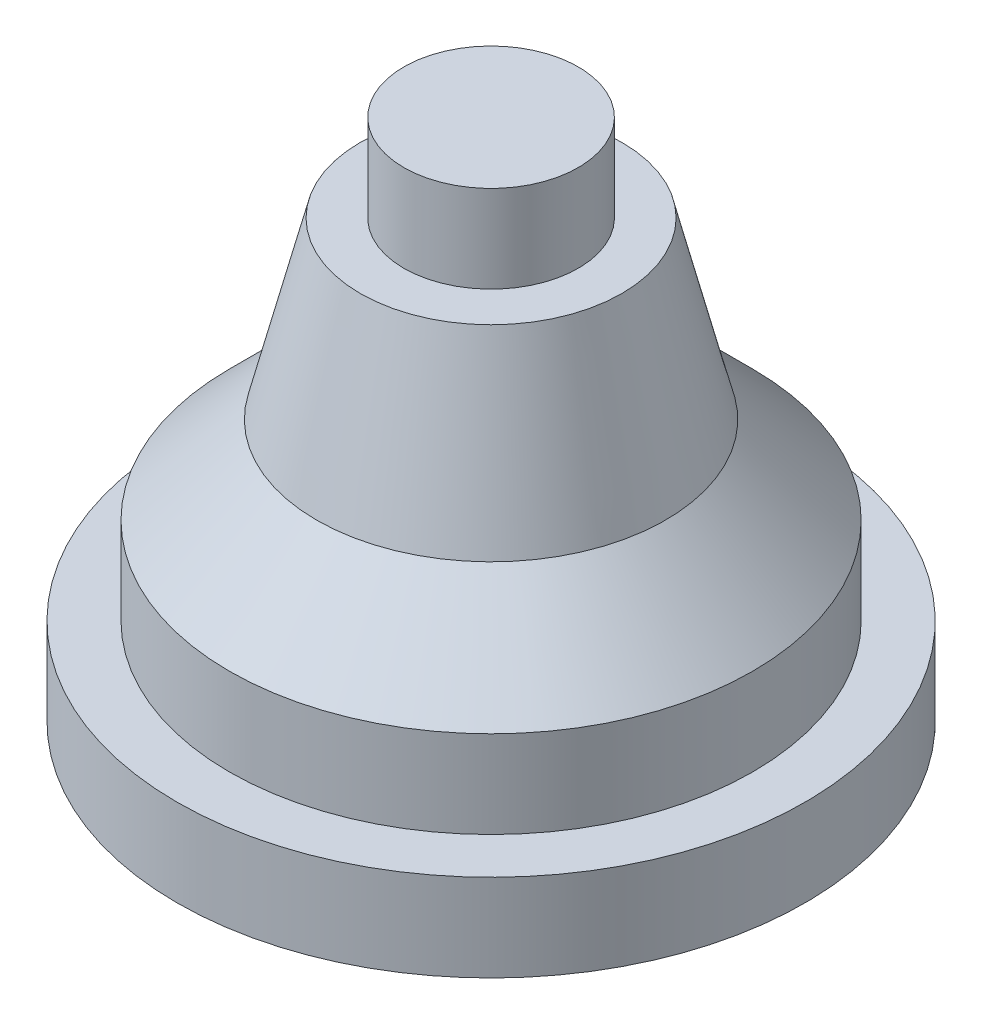
SolidWorks part; units mm, degrees
ref_plane "Plano frontal" through (0, 0, 0) normal (0, 0, 1) x (1, 0, 0)
ref_plane "Plano superior" through (0, 0, 0) normal (0, 1, 0) x (1, 0, 0)
ref_plane "Plano direito" through (0, 0, 0) normal (1, 0, 0) x (0, 0, -1)
sketch "Esboço1" plane through (0, 0, 0) normal (0, 0, 1) x (1, 0, 0)
  line L0 (0, 54.9096) -> (0, -50.9374) construction
  line L1 (0, 75) -> (25, 75)
  line L2 (25, 75) -> (25, 50)
  line L3 (25, 50) -> (37.5, 50)
  line L4 (37.5, 50) -> (50, 0)
  line L5 (50, 0) -> (75, -25)
  line L6 (75, -50) -> (75, -25)
  line L7 (75, -50) -> (90, -50)
  line L8 (90, -50) -> (90, -75)
  line L9 (90, -75) -> (0, -75)
  line L10 (0, -75) -> (0, 75)
  dimension "D1" = 25
  dimension "D2" = 25
  dimension "D3" = 37.5
  dimension "D4" = 75
  dimension "D5" = 90
  dimension "D6" = 150
  dimension "D7" = 125
  dimension "D8" = 75
  dimension "D9" = 75
  dimension "D10" = 50
  dimension "D11" = 100
revolve "Revolução1" add sketch "Esboço1" angle 360 about L0
